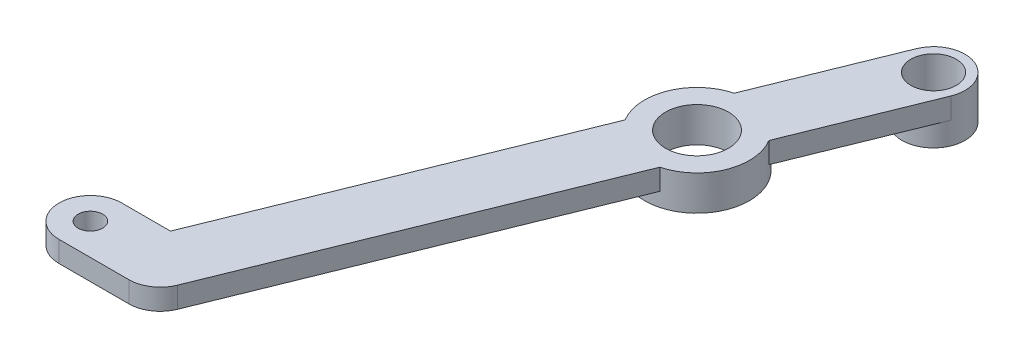
SolidWorks part; units mm, degrees
ref_plane "Front Plane" through (0, 0, 0) normal (0, 0, 1) x (1, 0, 0)
ref_plane "Top Plane" through (0, 0, 0) normal (0, 1, 0) x (1, 0, 0)
ref_plane "Right Plane" through (0, 0, 0) normal (1, 0, 0) x (0, 0, -1)
sketch "Sketch1" plane through (0, 0, 0) normal (0, 1, 0) x (1, 0, 0)
  line L0 (0, 4.5) -> (10, 4.5)
  line L1 (10, 4.5) -> (10, -4.5)
  line L2 (10, -4.5) -> (0, -4.5)
  line L3 (0, -4.5) -> (0, 4.5)
  circle A0 centre (0, 0) radius 4.5
  circle A1 centre (10, 0) radius 4.5
  circle A2 centre (0, 0) radius 1.75
  dimension "D1" = 9
  dimension "D2" = 9
  dimension "D4" = 3.5
  dimension "D3" = 10
extrude "Boss-Extrude1" add sketch "Sketch1" along normal blind 3
sketch "Sketch2" plane through (0, 3, 0) normal (0, 1, 0) x (1, 0, 0)
  line L0 (41.8932, 78.7897) -> (10, 0)
  line L1 (10, 0) -> (14.1712, -1.6885)
  line L2 (14.1712, -1.6885) -> (46.0645, 77.1013)
  line L3 (46.0645, 77.1013) -> (37.722, 80.4782)
  line L4 (37.722, 80.4782) -> (6.9669, 4.5)
  line L5 (0, 4.5) -> (10, 4.5) construction
  circle A0 centre (41.8932, 78.7897) radius 4.5
  arc A1 (10, -4.5) -> (10, 4.5) centre (10, 0) ccw construction
  circle A2 centre (0, 0) radius 1.75 construction
  arc A3 (6.9669, 4.5) -> (14.1712, -1.6885) centre (11.6118, 2.6198) ccw
  arc M4 (10, -4.5) -> (10, 4.5) centre (10, 0) ccw
  line M5 (10, 4.5) -> (0, 4.5)
  dimension "D1" = 9
  dimension "D2" = 62
  dimension "D3" = 85
extrude "Boss-Extrude2" add sketch "Sketch2" against normal blind 3 contours A3 L1 L0 M5 M4 | A0 L0 L2 M4 | L0 L1 M4 | A0 L4 L0 M5 M4 | L3 A0 | L0 A0 L3 | L3 A0 L0
sketch "Sketch3" plane through (0, 3, 0) normal (0, 1, 0) x (1, 0, 0)
  circle A0 centre (41.8932, 78.7897) radius 4.5
  circle A1 centre (41.8932, 78.7897) radius 3.25
  dimension "D1" = 6.5
extrude "Boss-Extrude3" add sketch "Sketch3" against normal blind 6.2
sketch "Sketch4" plane through (0, 3, 0) normal (0, 1, 0) x (1, 0, 0)
  circle A0 centre (41.8932, 78.7897) radius 3.25
extrude "Cut-Extrude1" cut sketch "Sketch4" against normal blind 3
sketch "Sketch5" plane through (0, 0, 0) normal (0, -1, 0) x (1, 0, 0)
  line L0 (14.1712, 1.6885) -> (46.0645, -77.1013) construction
  circle A0 centre (32.1377, -54.6893) radius 7.5
  circle A1 centre (41.8932, -78.7897) radius 3.25 construction
  dimension "D1" = 15
  dimension "D2" = 4.5
  dimension "D3" = 26
extrude "Boss-Extrude4" add sketch "Sketch5" against normal blind 3 and the other way blind 2
sketch "Sketch6" plane through (0, -2, 0) normal (0, -1, 0) x (1, 0, 0)
  circle A0 centre (32.1377, -54.6893) radius 4.5
  dimension "D1" = 9
extrude "Cut-Extrude2" cut sketch "Sketch6" against normal through all
equation "\"D2@Sketch1\"=\"D1@Sketch1\""
